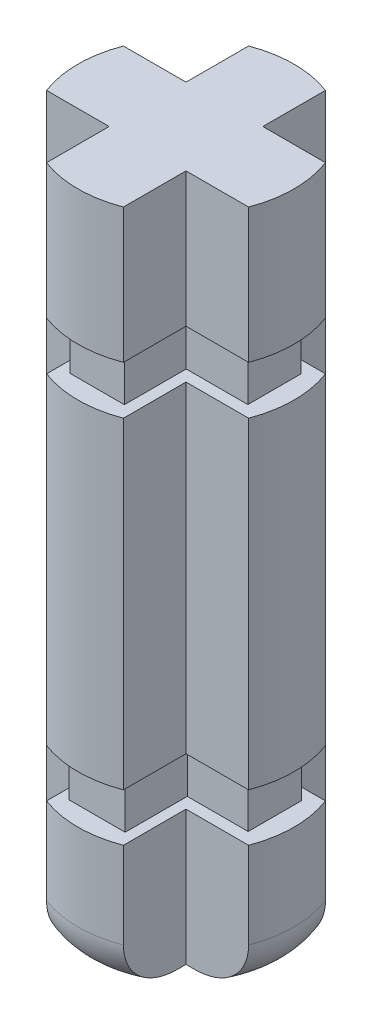
SolidWorks part; units mm, degrees
ref_plane "Front Plane" through (0, 0, 0) normal (0, 0, 1) x (1, 0, 0)
ref_plane "Top Plane" through (0, 0, 0) normal (0, 1, 0) x (1, 0, 0)
ref_plane "Right Plane" through (0, 0, 0) normal (1, 0, 0) x (0, 0, -1)
sketch "Sketch1" plane through (0, 0, 0) normal (0, 1, 0) x (1, 0, 0)
  line L0 (-0.8, -0.8) -> (-0.8, -2.103)
  line L1 (-0.8, 0.8) -> (-2.103, 0.8)
  line L2 (2.103, 0.8) -> (0.8, 0.8)
  line L3 (2.103, -0.8) -> (0.8, -0.8)
  line L4 (0.8, -0.8) -> (0.8, -2.103)
  line L5 (-0.8, -0.8) -> (-2.103, -0.8)
  line L8 (-0.8, 2.103) -> (-0.8, 0.8)
  line L9 (0.8, 2.103) -> (0.8, 0.8)
  arc A0 (-2.103, 0.8) -> (-2.103, -0.8) centre (0, 0) ccw
  arc A1 (0.8, 2.103) -> (-0.8, 2.103) centre (0, 0) ccw
  arc A2 (2.103, -0.8) -> (2.103, 0.8) centre (0, 0) ccw
  arc A3 (-0.8, -2.103) -> (0.8, -2.103) centre (0, 0) ccw
  point P26 (0.8, 0)
  dimension "D1" = 4.5
extrude "Boss-Extrude1" add sketch "Sketch1" along normal offset from surface (2.8 mm away) 2.8 contours L0 A3 L4 L3 A2 L2 L9 A1 L8 L1 A0 L5 up to plane "Top Plane"
fillet "Fillet1" radius 1 1 edges at (-2.25, 0, 0)
fillet "Fillet2" radius 1 1 edges at (0, 0, 2.25)
fillet "Fillet3" radius 1 1 edges at (2.25, 0, 0)
fillet "Fillet4" radius 1 1 edges at (0, 0, -2.25)
sketch "Sketch3" plane through (0, 2.8, 0) normal (0, 1, 0) x (1, 0, 0)
  line L0 (0, 2.2588) -> (0, 0)
  line L1 (0, -1.5905) -> (0, 1.5905) construction
  line L2 (-0.5834, 0.5563) -> (-0.5834, 1.85)
  line L3 (-1.85, -0.5563) -> (-0.5834, -0.5563)
  line L4 (-1.85, -0.5563) -> (-1.85, 0.5563)
  line L5 (-1.85, 0.5563) -> (-0.5834, 0.5563)
  line L6 (1.85, -0.5563) -> (1.85, 0.5563)
  line L8 (0.5834, 0.5563) -> (0.5834, 1.85)
  line L9 (0.5834, -1.85) -> (-0.5834, -1.85)
  line L10 (0.5834, -1.85) -> (0.5834, -0.5563)
  line L11 (0.5834, 1.85) -> (-0.5834, 1.85)
  line L12 (-0.5834, -1.85) -> (-0.5834, -0.5563)
  line L17 (0.5834, 0.5563) -> (1.85, 0.5563)
  line L18 (0.5834, -0.5563) -> (1.85, -0.5563)
  dimension "D1" = 3.7
  dimension "D2" = 3.7
extrude "Boss-Extrude2" add sketch "Sketch3" along normal blind 1
sketch "Sketch11" plane through (0, 3.8, 0) normal (0, 1, 0) x (1, 0, 0)
  line L0 (-0.799, -0.8003) -> (-0.799, -2.1033)
  line L1 (-0.799, 0.7997) -> (-2.102, 0.7997)
  line L2 (2.104, 0.7997) -> (0.801, 0.7997)
  line L3 (2.104, -0.8003) -> (0.801, -0.8003)
  line L4 (0.801, -0.8003) -> (0.801, -2.1033)
  line L5 (-0.799, -0.8003) -> (-2.102, -0.8003)
  line L6 (-0.799, 2.1027) -> (-0.799, 0.7997)
  line L7 (0.801, 2.1027) -> (0.801, 0.7997)
  arc A0 (-2.102, 0.7997) -> (-2.102, -0.8003) centre (0.001, -0.0003) ccw
  arc A1 (0.801, 2.1027) -> (-0.799, 2.1027) centre (0.001, -0.0003) ccw
  arc A2 (2.104, -0.8003) -> (2.104, 0.7997) centre (0.001, -0.0003) ccw
  arc A3 (-0.799, -2.1033) -> (0.801, -2.1033) centre (0.001, -0.0003) ccw
  point P13 (0.9292, -0.8003)
extrude "Boss-Extrude3" add sketch "Sketch11" along normal blind 6.7 contours A2 L2 L7 A1 L6 L1 A0 L5 L0 A3 L4 L3
sketch "Sketch12" plane through (0, 10.5, 0) normal (0, 1, 0) x (1, 0, 0)
  line L0 (0.5675, 0.5468) -> (1.85, 0.5468)
  line L1 (-1.85, 0.5468) -> (-0.5655, 0.5468)
  line L2 (-1.85, 0.5468) -> (-1.85, -0.5627)
  line L3 (-1.85, -0.5627) -> (-0.5655, -0.5627)
  line L4 (1.85, 0.5468) -> (1.85, -0.5627)
  line L5 (-0.5655, 0.5468) -> (-0.5655, 1.8497)
  line L6 (0.5675, 0.5468) -> (0.5675, 1.8497)
  line L7 (-0.5655, -1.8503) -> (0.5675, -1.8503)
  line L8 (-0.5655, -1.8503) -> (-0.5655, -0.5627)
  line L9 (-0.5655, 1.8497) -> (0.5675, 1.8497)
  line L10 (0.5675, -1.8503) -> (0.5675, -0.5627)
  line L11 (0.5675, -0.5627) -> (1.85, -0.5627)
  line L12 (0.0008, 0.0003) -> (0.001, -0.0003) construction
  line L13 (0, 0) -> (0.001, -0.0003) construction
  line L14 (0, 0) -> (0.0012, 0.0004) construction
  line L15 (0.001, -0.0003) -> (0.0012, 0.0004) construction
  point P0 (0, 0)
  point P6 (0.001, -0.0003)
  dimension "D1" = 3.7
  dimension "D2" = 3.7
extrude "Boss-Extrude4" add sketch "Sketch12" along normal blind 1
sketch "Sketch13" plane through (0, 11.5, 0) normal (0, 1, 0) x (1, 0, 0)
  line L0 (-0.8061, -0.7936) -> (-0.8061, -2.0966)
  line L1 (-0.8061, 0.8064) -> (-2.109, 0.8064)
  line L2 (2.0969, 0.8064) -> (0.7939, 0.8064)
  line L3 (2.0969, -0.7936) -> (0.7939, -0.7936)
  line L4 (0.7939, -0.7936) -> (0.7939, -2.0966)
  line L5 (-0.8061, -0.7936) -> (-2.109, -0.7936)
  line L6 (-0.8061, 2.1094) -> (-0.8061, 0.8064)
  line L7 (0.7939, 2.1094) -> (0.7939, 0.8064)
  arc A0 (-2.109, 0.8064) -> (-2.109, -0.7936) centre (-0.0061, 0.0064) ccw
  arc A1 (0.7939, 2.1094) -> (-0.8061, 2.1094) centre (-0.0061, 0.0064) ccw
  arc A2 (2.0969, -0.7936) -> (2.0969, 0.8064) centre (-0.0061, 0.0064) ccw
  arc A3 (-0.8061, -2.0966) -> (0.7939, -2.0966) centre (-0.0061, 0.0064) ccw
  point P13 (0.9221, -0.7936)
extrude "Boss-Extrude5" add sketch "Sketch13" along normal blind 2.8
